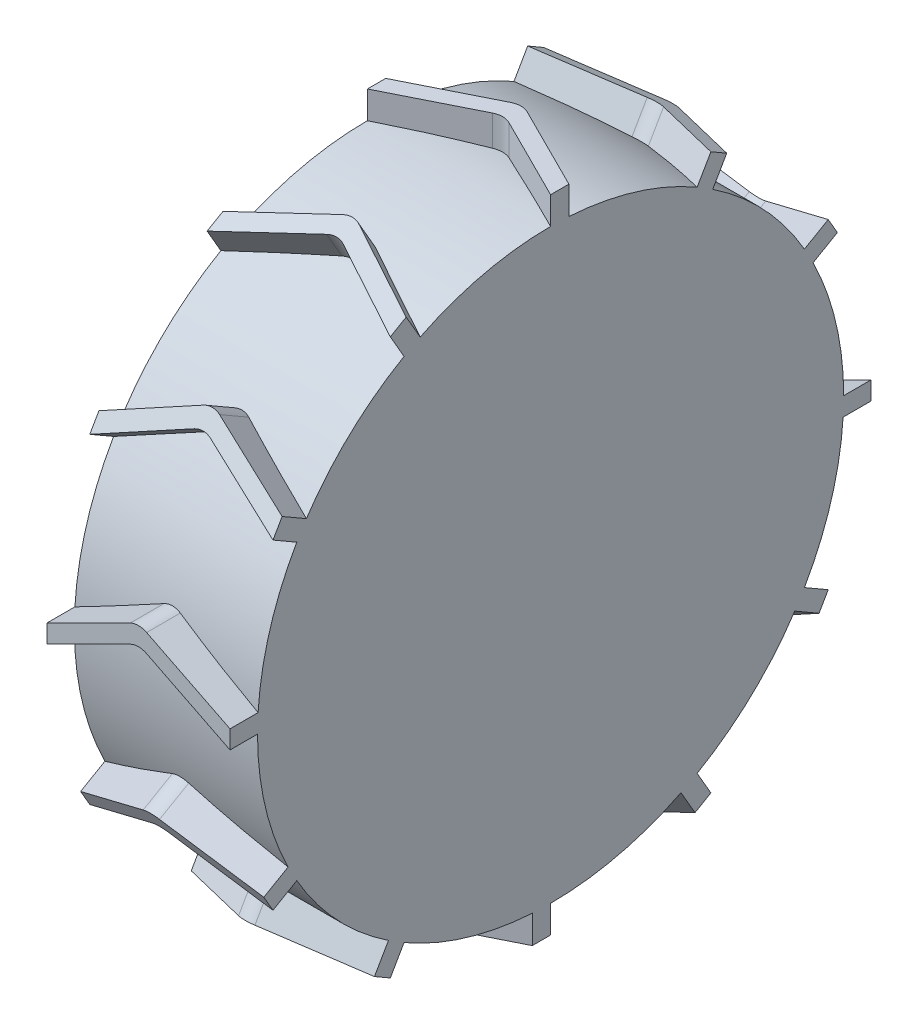
SolidWorks part; units mm, degrees
ref_plane "Front Plane" through (0, 0, 0) normal (0, 0, 1) x (1, 0, 0)
ref_plane "Top Plane" through (0, 0, 0) normal (0, 1, 0) x (1, 0, 0)
ref_plane "Right Plane" through (0, 0, 0) normal (1, 0, 0) x (0, 0, -1)
sketch "Sketch2" plane through (0, 0, 0) normal (1, 0, 0) x (0, 0, -1)
  circle A2 centre (0, 0) radius 159.9966
extrude "Boss-Extrude1" add sketch "Sketch2" along normal blind 100
sketch "Sketch4" plane through (0, 0, 0) normal (0, 1, 0) x (1, 0, 0)
  line L8 (0, 0) -> (100, 0) construction
  line L9 (100, -159.9966) -> (100, 159.9966) construction
  line L10 (0, 0) -> (45.5279, 22.7639)
  line L11 (54.4721, 22.7639) -> (100, 0)
  line L12 (100, 0) -> (100, 10)
  line L13 (100, 10) -> (54.4721, 32.7639)
  line L14 (45.5279, 32.7639) -> (0, 10)
  line L15 (0, 159.9966) -> (0, -159.9966) construction
  line L16 (0, 10) -> (0, 0)
  arc A0 (54.4721, 32.7639) -> (45.5279, 32.7639) centre (50, 23.8197) ccw
  arc A1 (45.5279, 22.7639) -> (54.4721, 22.7639) centre (50, 13.8197) cw
  point P4 (50, 0)
  point P12 (0, 0)
  point P13 (0, 0)
  point P14 (15.575, 9.3556)
  point P15 (0, 0)
  point P18 (50, 35)
  point P21 (50, 25)
  dimension "D3" = 10
  dimension "D1" = 10
  dimension "D2" = 10
  dimension "D4" = 25
extrude "Boss-Extrude2" add sketch "Sketch4" along normal blind 175
pattern_circular "CirPattern2" count 12 over 360 about axis through (0, 0, 0) along (1, 0, 0) of "Boss-Extrude2"
